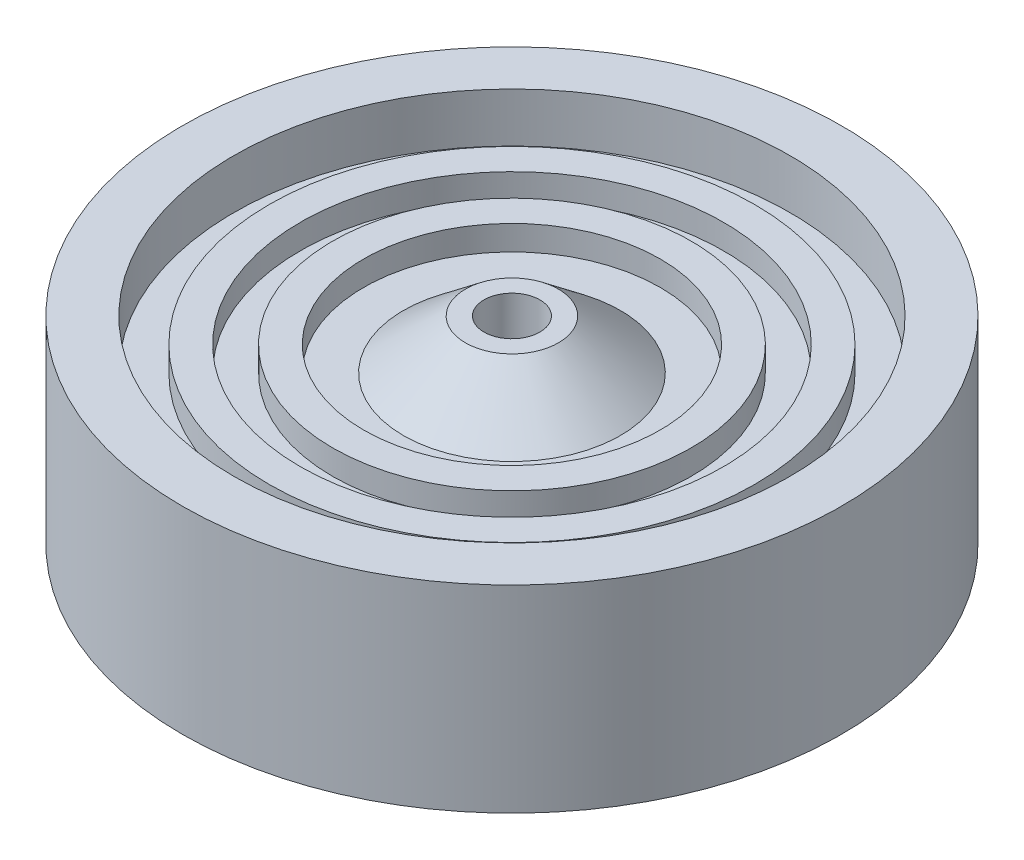
SolidWorks part; units mm, degrees
ref_plane "Front Plane" through (0, 0, 0) normal (0, 0, 1) x (1, 0, 0)
ref_plane "Top Plane" through (0, 0, 0) normal (0, 1, 0) x (1, 0, 0)
ref_plane "Right Plane" through (0, 0, 0) normal (1, 0, 0) x (0, 0, -1)
sketch "Sketch5" plane through (0, 0, 0) normal (0, 0, 1) x (1, 0, 0)
sketch "Sketch7" plane through (0, 0, 0) normal (0, 0, 1) x (1, 0, 0)
  line L0 (-50.8118, 150.5988) -> (-50.8118, 6.53) construction
sketch "Sketch8" plane through (0, 0, 0) normal (0, 0, 1) x (1, 0, 0)
  line L0 (-50.8118, 78.5644) -> (-156.2681, 78.5644) construction
  line L1 (-50.8118, 150.5988) -> (-50.8118, 6.53) construction
  line L3 (-62.2704, 102.8935) -> (-77.5215, 90.729)
  line L4 (-77.5215, 90.729) -> (-87.3257, 90.729)
  line L5 (-87.3257, 90.729) -> (-87.3257, 96.8112)
  line L6 (-87.3257, 96.8112) -> (-94.9457, 96.8112)
  line L7 (-94.9457, 96.8112) -> (-94.9457, 90.729)
  line L8 (-94.9457, 90.729) -> (-102.9344, 90.729)
  line L9 (-102.9344, 90.729) -> (-102.9344, 96.8112)
  line L10 (-102.9344, 96.8112) -> (-110.5544, 96.8112)
  line L11 (-110.5544, 96.8112) -> (-110.5544, 90.729)
  line L12 (-110.5544, 90.729) -> (-119.2693, 90.729)
  line L13 (-119.2693, 90.729) -> (-119.2693, 102.8935)
  line L14 (-119.2693, 102.8935) -> (-131.9693, 102.8935)
  line L15 (-131.9693, 102.8935) -> (-131.9693, 54.2353)
  line L17 (-119.2693, 54.2353) -> (-131.9693, 54.2353)
  line L18 (-119.2693, 66.3999) -> (-119.2693, 54.2353)
  line L19 (-110.5544, 66.3999) -> (-119.2693, 66.3999)
  line L20 (-110.5544, 60.3176) -> (-110.5544, 66.3999)
  line L21 (-102.9344, 60.3176) -> (-110.5544, 60.3176)
  line L22 (-102.9344, 66.3999) -> (-102.9344, 60.3176)
  line L23 (-94.9457, 66.3999) -> (-102.9344, 66.3999)
  line L24 (-94.9457, 60.3176) -> (-94.9457, 66.3999)
  line L25 (-87.3257, 60.3176) -> (-94.9457, 60.3176)
  line L26 (-87.3257, 66.3999) -> (-87.3257, 60.3176)
  line L27 (-77.5215, 66.3999) -> (-87.3257, 66.3999)
  line L28 (-62.2704, 54.2353) -> (-77.5215, 66.3999)
  line L29 (-62.2704, 102.8935) -> (-57.696, 102.8935)
  line L30 (-57.696, 102.8935) -> (-57.696, 54.2353)
  line L31 (-57.696, 54.2353) -> (-62.2704, 54.2353)
  dimension "D1" = 12.7
  dimension "D2" = 7.62
  dimension "D3" = 7.62
  dimension "D4" = 6.8842
sketch "Sketch9" plane through (0, 0, 0) normal (0, 0, 1) x (1, 0, 0)
sketch "Sketch10" plane through (0, 0, 0) normal (0, 0, 1) x (1, 0, 0)
sketch "Sketch11" plane through (0, 0, 0) normal (0, 0, 1) x (1, 0, 0)
sketch "Sketch12" plane through (0, 0, 0) normal (0, 0, 1) x (1, 0, 0)
sketch "Sketch13" plane through (0, 0, 0) normal (0, 0, 1) x (1, 0, 0)
revolve "Revolve3" add sketch "Sketch8" angle 360 about L0
